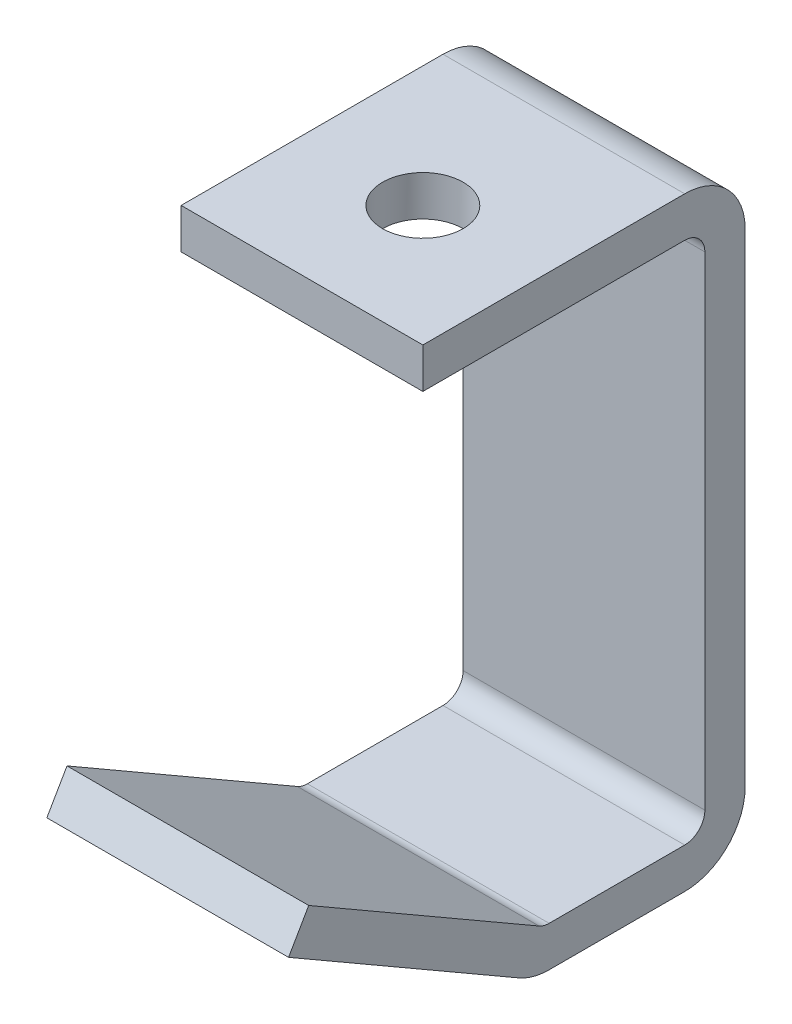
SolidWorks part; units mm, degrees
ref_plane "front" through (0, 0, 0) normal (0, 0, 1) x (1, 0, 0)
ref_plane "top" through (0, 0, 0) normal (0, 1, 0) x (1, 0, 0)
ref_plane "right" through (0, 0, 0) normal (1, 0, 0) x (0, 0, -1)
sketch "Sketch1" plane through (0, 0, 0) normal (1, 0, 0) x (0, 0, -1)
  line L0 (0, 0) -> (0, 82.55)
  line L1 (0, 82.55) -> (-44.45, 82.55)
  line L4 (-62.443, 21.3868) -> (-25.4, 0)
  line L5 (-25.4, 0) -> (0, 0)
  dimension "D1" = 82.55
  dimension "D2" = 44.45
  dimension "D3" = 30
  dimension "D4" = 42.7736
  dimension "D5" = 25.4
extrude "Base-Extrude-Thin" add sketch "Sketch1" along normal mid plane 38.1 thin
sketch "Sketch2" plane through (0, 88.9, 0) normal (0, 1, 0) x (-1, 0, 0)
  line L0 (0, 50) -> (0, -50) construction
  line L1 (-19.05, 44.45) -> (19.05, 44.45) construction
  circle A0 centre (0, 25.4) radius 6.35
  dimension "D1" = 12.7
  dimension "D2" = 19.05
extrude "Cut-Extrude1" cut sketch "Sketch2" against normal up to next
